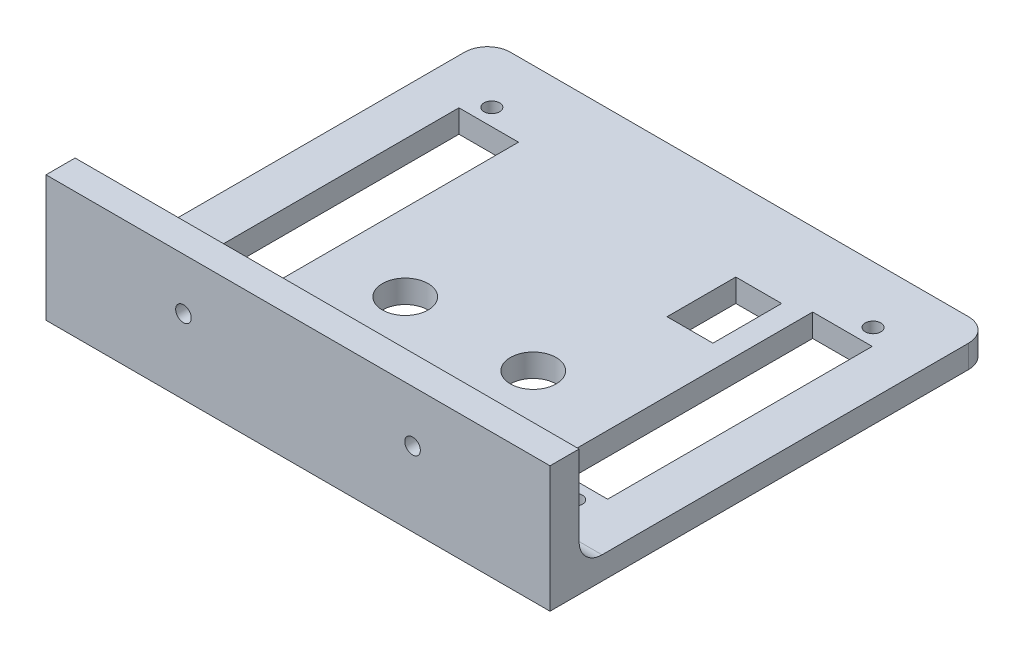
SolidWorks part; units mm, degrees
ref_plane "Front Plane" through (0, 0, 0) normal (0, 0, 1) x (1, 0, 0)
ref_plane "Top Plane" through (0, 0, 0) normal (0, 1, 0) x (1, 0, 0)
ref_plane "Right Plane" through (0, 0, 0) normal (1, 0, 0) x (0, 0, -1)
sketch "Sketch1" plane through (0, 0, 0) normal (0, 1, 0) x (1, 0, 0)
  line L1 (0, 0) -> (110, 0)
  line L2 (0, 0) -> (0, -90)
  line L3 (0, -90) -> (110, -90)
  line L4 (110, 0) -> (110, -90)
  dimension "D1" = 110
  dimension "D2" = 90
extrude "Boss-Extrude1" add sketch "Sketch1" along normal mid plane 5
sketch "Sketch3" plane through (0, 2.5, 0) normal (0, 1, 0) x (1, 0, 0)
  line L0 (55, 0) -> (55, -6.1118) construction
  line L1 (13.4, -77.5576) -> (96.6, -77.5576) construction
  line L2 (13.4, -77.5576) -> (13.4, -12.4424) construction
  line L3 (13.4, -12.4424) -> (96.6, -12.4424) construction
  line L4 (96.6, -77.5576) -> (96.6, -12.4424) construction
  line L5 (13.4, -77.5576) -> (96.6, -12.4424) construction
  line L6 (13.4, -12.4424) -> (96.6, -77.5576) construction
  line L7 (110, 0) -> (0, 0) construction
  line L8 (0, -45) -> (5.6534, -45) construction
  line L9 (0, 0) -> (0, -90) construction
  point P0 (55, -45)
  point P14 (96.6, -12.4424)
  point P15 (96.6, -77.5576)
  point P16 (13.4, -12.4424)
  point P17 (13.4, -77.5576)
  dimension "D1" = 83.2
  dimension "D2" = 65.1151
hole_wizard "M3 Clearance Hole1" positions "Sketch3" profile "Sketch4" hole size "M3" standard "ANSI Metric"
sketch "Sketch4" plane through (13.4, 2.5, 77.5576) normal (1, 0, 0) x (0, 0, 1)
  line L0 (0, 0) -> (0, 5)
  line L1 (0, 5) -> (1.7, 5)
  line L2 (1.7, 5) -> (1.7, 0)
  line L5 (1.7, 0) -> (0, 0)
  line L11 (0, -6.35) -> (0, 107.95) construction
  dimension "Thru Hole Dia." = 3.4
  dimension "Thru Hole Depth" = 5
sketch "Sketch5" plane through (0, 0, 0) normal (0, 1, 0) x (1, 0, 0)
  line L0 (110, -90) -> (110, 0) construction
  line L1 (0, -90) -> (110, -90)
  line L2 (0, -90) -> (0, -96.35)
  line L3 (0, -96.35) -> (110, -96.35)
  line L4 (110, -90) -> (110, -96.35)
  dimension "D1" = 6.35
extrude "Boss-Extrude2" add sketch "Sketch5" along normal blind 25 and the other way up to surface (2.5 mm away) other way up to face at (96.6, -2.5, 14.1424)
sketch "Sketch6" plane through (0, 0, 90) normal (0, 0, -1) x (-1, 0, 0)
  line L0 (0, 13.75) -> (-110, 13.75) construction
  line L1 (0, 2.5) -> (0, 25) construction
  line L2 (-110, 2.5) -> (-110, 25) construction
  line L3 (-55, 25) -> (-55, 2.5) construction
  line L4 (-110, 25) -> (0, 25) construction
  line L5 (-110, 2.5) -> (0, 2.5) construction
  point P12 (-30, 13.75)
  point P13 (-80, 13.75)
  dimension "D1" = 50
hole_wizard "CBORE for M3 SHCS1" positions "Sketch6" profile "Sketch7" counterbore size "M3" standard "ANSI Metric" end condition up to next
sketch "Sketch7" plane through (80, 13.75, 90) normal (1, 0, 0) x (0, 1, 0)
  line L0 (0, 0) -> (0, 6.35)
  line L1 (0, 6.35) -> (1.7, 6.35)
  line L3 (1.7, 6.35) -> (1.7, 3)
  line L4 (1.7, 3) -> (3.25, 3)
  line L5 (3.25, 3) -> (3.25, 0)
  line L7 (3.25, 0) -> (0, 0)
  line L11 (0, -6.35) -> (0, 107.95) construction
  dimension "Thru Hole Dia." = 3.4
  dimension "Thru Hole Depth" = 6.35
  dimension "C'Bore Dia." = 6.5
  dimension "C'Bore Depth" = 3
sketch "Sketch8" plane through (0, 2.5, 0) normal (0, 1, 0) x (1, 0, 0)
  line L0 (55, 0) -> (55, -10.0728) construction
  line L1 (9.9, -9.9) -> (100.1, -9.9) construction
  line L2 (9.9, -9.9) -> (9.9, -80.1) construction
  line L3 (9.9, -80.1) -> (100.1, -80.1) construction
  line L4 (100.1, -9.9) -> (100.1, -80.1) construction
  line L5 (9.9, -9.9) -> (100.1, -80.1) construction
  line L6 (9.9, -80.1) -> (100.1, -9.9) construction
  line L7 (110, 0) -> (0, 0) construction
  line L8 (0, -45) -> (9.6679, -45) construction
  line L9 (0, 0) -> (0, -90) construction
  line L10 (100.1, -16.1262) -> (92.1, -16.1262) construction
  line L11 (9.9, -9.9) -> (17.9, -9.9) construction
  line L12 (9.9, -9.9) -> (9.9, -16.1262) construction
  line L13 (9.9, -16.1262) -> (17.9, -16.1262) construction
  line L14 (17.9, -9.9) -> (17.9, -16.1262) construction
  line L15 (92.1, -9.9) -> (92.1, -16.1262) construction
  line L16 (92.1, -80.1) -> (92.1, -73.8738) construction
  line L17 (100.1, -73.8738) -> (92.1, -73.8738) construction
  line L18 (17.9, -80.1) -> (17.9, -73.8738) construction
  line L19 (9.9, -73.8738) -> (17.9, -73.8738) construction
  line L20 (17.9, -9.9) -> (92.1, -9.9)
  line L21 (92.1, -9.9) -> (92.1, -16.1262)
  line L22 (92.1, -16.1262) -> (100.1, -16.1262)
  line L23 (100.1, -16.1262) -> (100.1, -73.8738)
  line L24 (100.1, -73.8738) -> (92.1, -73.8738)
  line L25 (92.1, -73.8738) -> (92.1, -80.1)
  line L26 (92.1, -80.1) -> (17.9, -80.1)
  line L27 (17.9, -80.1) -> (17.9, -73.8738)
  line L28 (17.9, -73.8738) -> (9.9, -73.8738)
  line L29 (9.9, -73.8738) -> (9.9, -16.1262)
  line L30 (9.9, -16.1262) -> (17.9, -16.1262)
  line L31 (17.9, -16.1262) -> (17.9, -9.9)
  point P0 (55, -45)
  dimension "D1" = 90.2
  dimension "D2" = 70.2
  dimension "D3" = 8
extrude "Cut-Extrude1" cut sketch "Sketch8" against normal through all
sketch "Sketch9" plane through (0, 2.5, 0) normal (0, 1, 0) x (1, 0, 0)
  line L0 (17.9, -16.1262) -> (92.1, -73.8738) construction
  line L1 (92.1, -16.1262) -> (17.9, -73.8738) construction
  line L2 (17.9, -12.9583) -> (55, -41.8321)
  line L3 (17.9, -9.9) -> (17.9, -16.1262) construction
  line L4 (92.1, -73.8738) -> (100.1, -73.8738) construction
  line L5 (17.9, -12.9583) -> (17.9, -16.1262)
  line L6 (17.9, -16.1262) -> (13.8296, -16.1262)
  line L7 (17.9, -16.1262) -> (9.9, -16.1262) construction
  line L8 (13.8296, -16.1262) -> (50.9296, -45)
  line L9 (92.1, -80.1) -> (92.1, -73.8738) construction
  line L10 (92.1, -77.0417) -> (92.1, -73.8738)
  line L11 (92.1, -73.8738) -> (96.1704, -73.8738)
  line L12 (92.1, -12.9583) -> (55, -41.8321)
  line L13 (92.1, -16.1262) -> (92.1, -9.9) construction
  line L14 (9.9, -73.8738) -> (17.9, -73.8738) construction
  line L15 (96.1704, -16.1262) -> (59.0704, -45)
  line L16 (100.1, -16.1262) -> (92.1, -16.1262) construction
  line L17 (17.9, -73.8738) -> (17.9, -80.1) construction
  line L18 (17.9, -77.0417) -> (17.9, -73.8738)
  line L19 (17.9, -73.8738) -> (13.8296, -73.8738)
  line L20 (92.1, -12.9583) -> (92.1, -16.1262)
  line L21 (92.1, -16.1262) -> (96.1704, -16.1262)
  line L22 (59.0704, -45) -> (96.1704, -73.8738)
  line L23 (55, -48.1679) -> (92.1, -77.0417)
  line L24 (50.9296, -45) -> (13.8296, -73.8738)
  line L25 (55, -48.1679) -> (17.9, -77.0417)
  dimension "D1" = 2.5
  dimension "D2" = 2.5
  dimension "D3" = 2.5
  dimension "D4" = 2.5
extrude "Boss-Extrude3" [suppressed] add sketch "Sketch9" against normal through all
sketch "Sketch10" plane through (0, 2.5, 0) normal (0, 1, 0) x (1, 0, 0)
  line L10 (17.9, -9.9) -> (92.1, -9.9)
  line L11 (17.9, -9.9) -> (17.9, -80.1)
  line L12 (17.9, -80.1) -> (92.1, -80.1)
  line L13 (92.1, -9.9) -> (92.1, -80.1)
  line L14 (92.1, -9.9) -> (17.9, -9.9) construction
  line L15 (17.9, -9.9) -> (17.9, -16.1262) construction
  line L16 (92.1, -16.1262) -> (92.1, -9.9) construction
  line L17 (17.9, -80.1) -> (92.1, -80.1) construction
  line L18 (100.1, -73.8738) -> (100.1, -16.1262) construction
  line L19 (72.1, -17.9) -> (82.1, -17.9)
  line L20 (72.1, -17.9) -> (72.1, -32.9)
  line L21 (72.1, -32.9) -> (82.1, -32.9)
  line L22 (82.1, -17.9) -> (82.1, -32.9)
  circle A0 centre (39.76, -57.7075) radius 5
  circle A1 centre (67.7, -57.7075) radius 5
  circle A2 centre (13.4, -77.5576) radius 1.7 construction
  point P27 (0, 0)
  point P28 (0, 0)
  dimension "D5" = 26.36
  dimension "D7" = 19.85
  dimension "D8" = 10
  dimension "D1" = 8
  dimension "D2" = 15
  dimension "D3" = 10
  dimension "D4" = 18
  dimension "D6" = 27.94
extrude "Boss-Extrude4" add sketch "Sketch10" against normal through all
sketch "Sketch11" plane through (0, 2.5, 0) normal (0, 1, 0) x (1, 0, 0)
  line L0 (9.9, -73.8738) -> (17.9, -73.8738) construction
  line L1 (17.9, -16.1262) -> (22.9, -16.1262)
  line L2 (17.9, -16.1262) -> (17.9, -73.8738)
  line L3 (17.9, -73.8738) -> (22.9, -73.8738)
  line L4 (22.9, -16.1262) -> (22.9, -73.8738)
  line L5 (92.1, -73.8738) -> (100.1, -73.8738) construction
  line L6 (92.1, -16.1262) -> (87.1, -16.1262)
  line L7 (92.1, -16.1262) -> (92.1, -73.8738)
  line L8 (92.1, -73.8738) -> (87.1, -73.8738)
  line L9 (87.1, -16.1262) -> (87.1, -73.8738)
  dimension "D1" = 5
  dimension "D2" = 5
extrude "Cut-Extrude2" cut sketch "Sketch11" against normal through all
fillet "Fillet1" radius 5 3 edges at (55, 2.5, 90) (110, 0, 0) (0, 0, 0)
equation "\"D2@Sketch9\"=\"D1@Sketch9\""
equation "\"D3@Sketch9\"=\"D1@Sketch9\""
equation "\"D4@Sketch9\"=\"D1@Sketch9\""
equation "\"D2@Sketch11\"=\"D1@Sketch11\""
